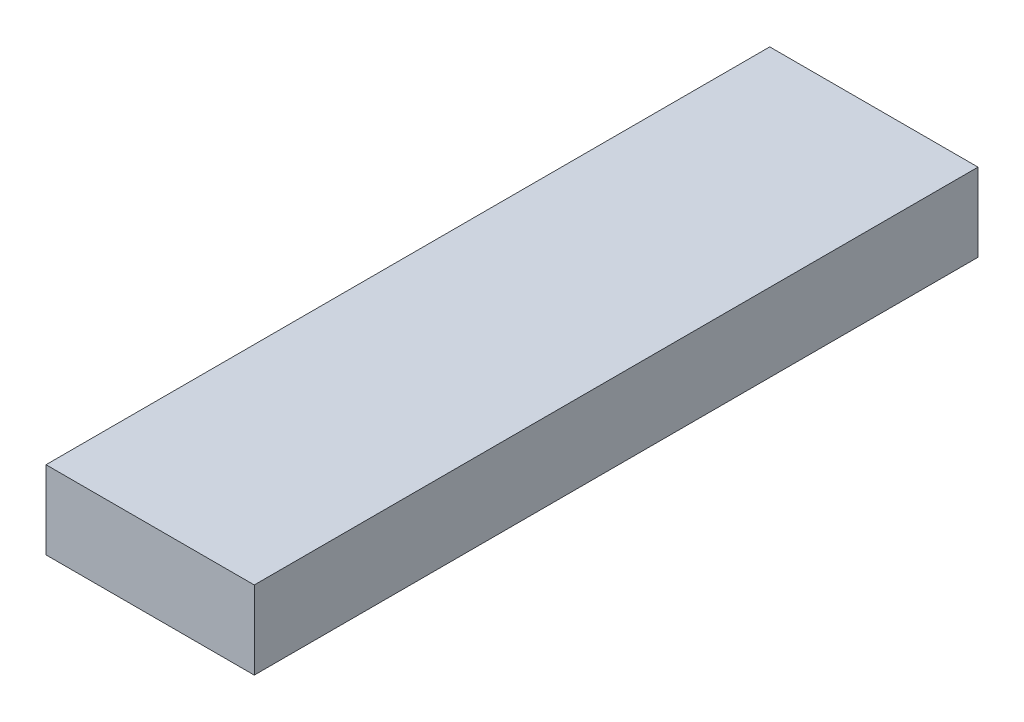
SolidWorks part; units mm, degrees
material "Простая углеродистая сталь"
ref_plane "Спереди" through (0, 0, 0) normal (0, 0, 1) x (1, 0, 0)
ref_plane "Сверху" through (0, 0, 0) normal (0, 1, 0) x (1, 0, 0)
ref_plane "Справа" through (0, 0, 0) normal (1, 0, 0) x (0, 0, -1)
sketch "Эскиз1" plane through (0, 0, 0) normal (0, 1, 0) x (1, 0, 0)
  line L1 (0, 0) -> (80, 0)
  line L2 (0, 0) -> (0, 278)
  line L3 (0, 278) -> (80, 278)
  line L4 (80, 0) -> (80, 278)
extrude "Бобышка-Вытянуть1" add sketch "Эскиз1" along normal blind 30
